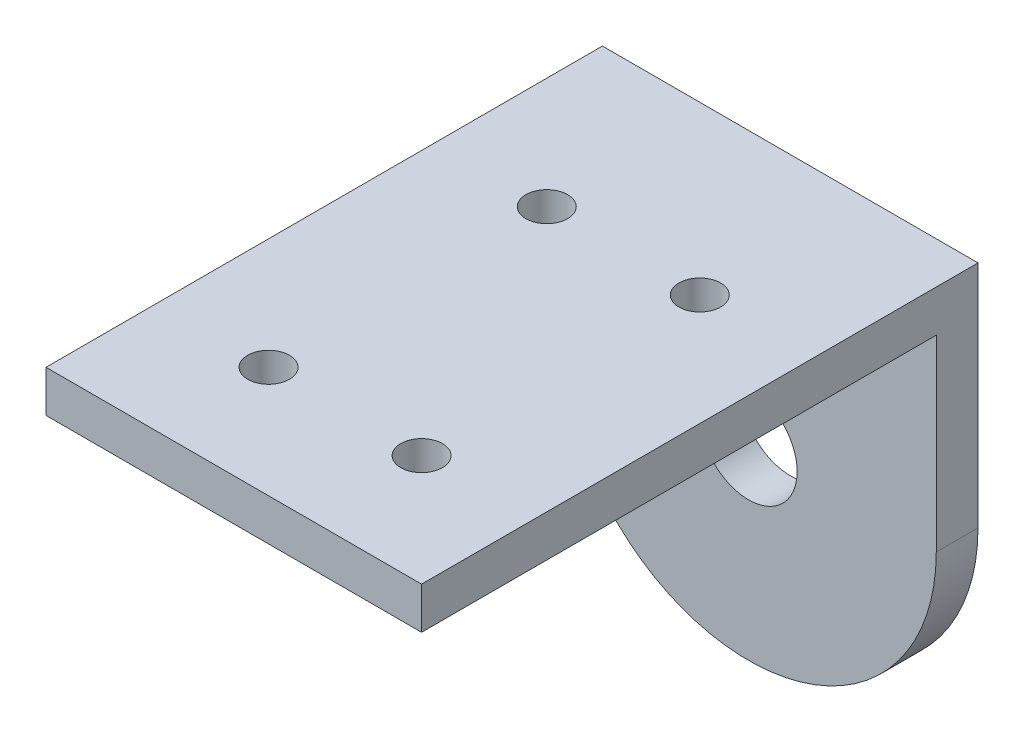
SolidWorks part; units mm, degrees
ref_plane "前视基准面" through (0, 0, 0) normal (0, 0, 1) x (1, 0, 0)
ref_plane "上视基准面" through (0, 0, 0) normal (0, 1, 0) x (1, 0, 0)
ref_plane "右视基准面" through (0, 0, 0) normal (1, 0, 0) x (0, 0, -1)
sketch "Model" plane through (0, 0, 0) normal (0, 0, 1) x (1, 0, 0)
  line L0 (2619.7667, 1592.8264) -> (2619.7667, 1609.3264)
  line L1 (2592.7667, 1592.8264) -> (2592.7667, 1609.3264)
  line L2 (2592.7667, 1609.3264) -> (2619.7667, 1609.3264)
  circle A0 centre (2606.2667, 1592.8264) radius 3.5
  arc A1 (2592.7667, 1592.8264) -> (2619.7667, 1592.8264) centre (2606.2667, 1592.8264) ccw
  dimension "D1" = 16.5
extrude "凸台-拉伸1" add sketch "Model" along normal blind 40
sketch "草图3" plane through (2619.7667, 0, 0) normal (1, 0, 0) x (0, 0, -1)
  line L0 (-40, 1592.8264) -> (-40, 1609.3264) construction
  line L1 (-40, 1606.3264) -> (-3, 1606.3264)
  line L2 (-40, 1606.3264) -> (-40, 1569.3264)
  line L3 (-40, 1569.3264) -> (-3, 1569.3264)
  line L4 (-3, 1606.3264) -> (-3, 1569.3264)
  line L5 (-40, 1609.3264) -> (0, 1609.3264) construction
  line L6 (0, 1592.8264) -> (0, 1609.3264) construction
  dimension "D1" = 3
  dimension "D2" = 3
  dimension "D3" = 40
extrude "切除-拉伸1" cut sketch "草图3" against normal blind 40
sketch "草图4" plane through (0, 1609.3264, 0) normal (0, 1, 0) x (1, 0, 0)
  line L6 (2619.7667, -40) -> (2619.7667, -32)
  circle A0 centre (2600.7667, -32) radius 1.5
  circle A1 centre (2611.7667, -32) radius 1.5
  circle A2 centre (2600.7667, -12) radius 1.5
  circle A3 centre (2611.7667, -12) radius 1.5
  dimension "D7" = 3
  dimension "D8" = 3
  dimension "D9" = 3
  dimension "D10" = 3
extrude "切除-拉伸2" cut sketch "草图4" against normal blind 40 contours A0 | A1 | A3 | A2
